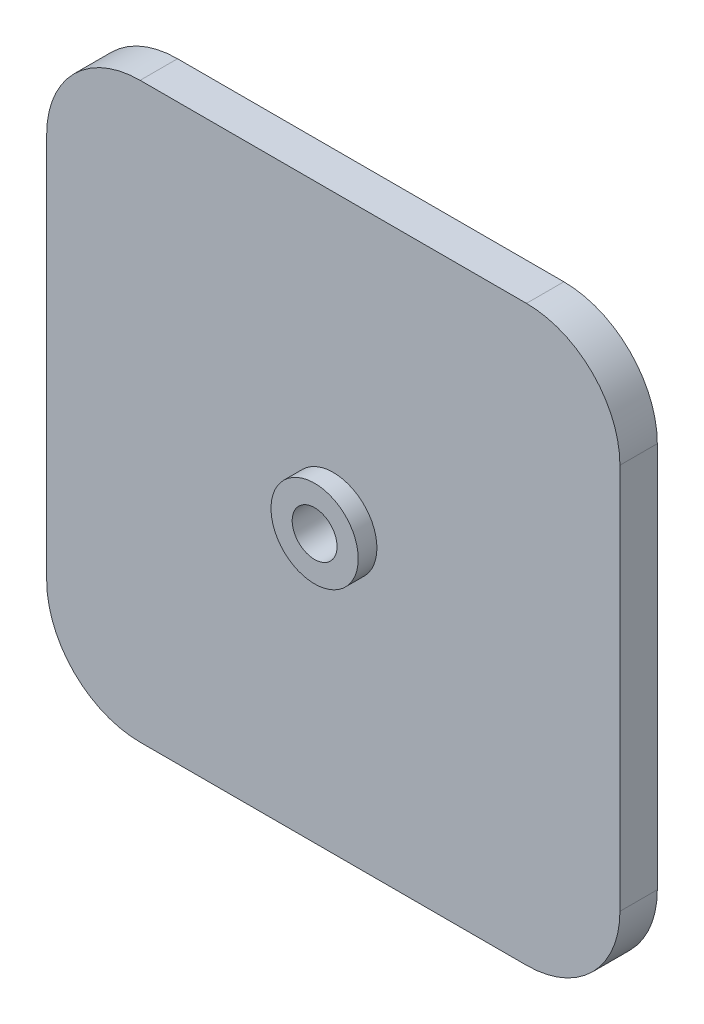
SolidWorks part; units mm, degrees
ref_plane "Plano frontal" through (0, 0, 0) normal (0, 0, 1) x (1, 0, 0)
ref_plane "Plano superior" through (0, 0, 0) normal (0, 1, 0) x (1, 0, 0)
ref_plane "Plano direito" through (0, 0, 0) normal (1, 0, 0) x (0, 0, -1)
sketch "Sketch1" plane through (0, 0, 0) normal (0, 0, 1) x (1, 0, 0)
  line L1 (-15.5, 23) -> (15.5, 23)
  line L2 (-23, 15.5) -> (-23, -15.5)
  line L3 (-15.5, -23) -> (15.5, -23)
  line L4 (23, 15.5) -> (23, -15.5)
  line L5 (-23, 23) -> (23, -23) construction
  line L6 (-23, -23) -> (23, 23) construction
  arc A0 (-23, -15.5) -> (-15.5, -23) centre (-15.5, -15.5) ccw
  arc A1 (15.5, -23) -> (23, -15.5) centre (15.5, -15.5) ccw
  arc A2 (15.5, 23) -> (23, 15.5) centre (15.5, 15.5) cw
  arc A3 (-15.5, 23) -> (-23, 15.5) centre (-15.5, 15.5) ccw
  point P0 (0, 0)
  dimension "D3" = 7.5
  dimension "D1" = 46
  dimension "D2" = 46
extrude "Boss-Extrude1" add sketch "Sketch1" along normal blind 3
sketch "Sketch2" plane through (0, 0, 3) normal (0, 0, 1) x (1, 0, 0)
  circle A0 centre (0, 0) radius 3.5
  dimension "D1" = 7
extrude "Boss-Extrude2" add sketch "Sketch2" along normal blind 1.5
hole_wizard "M3 Clearance Hole1" positions "3DSketch1" profile "Sketch3" hole size "M3" standard "ANSI Metric" end condition through all
sketch3d "3DSketch1"
  line L0 (0, 0, 4.5) -> (0, 0, 3) construction
  point P0 (0, 0, 0)
  point P4 (0, 0, 4.5)
  point P5 (0, 0, 4.5)
sketch "Sketch3" plane through (0, 0, 4.5) normal (1, 0, 0) x (0, -1, 0)
  line L0 (0, 0) -> (0, 4.5)
  line L1 (0, 4.5) -> (1.8, 4.5)
  line L2 (1.8, 4.5) -> (1.8, 0)
  line L5 (1.8, 0) -> (0, 0)
  line L11 (0, -6.35) -> (0, 107.95) construction
  dimension "Thru Hole Dia." = 3.6
  dimension "Thru Hole Depth" = 4.5
